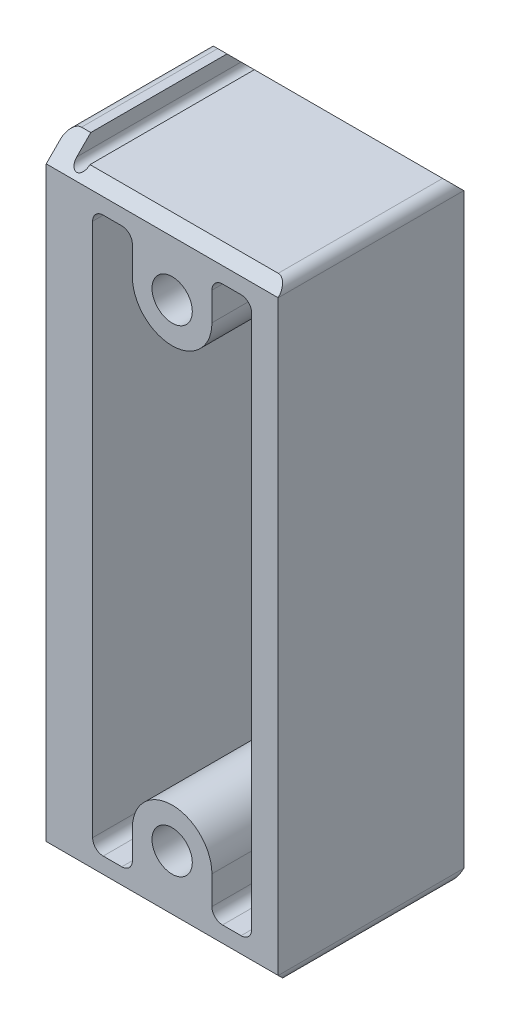
SolidWorks part; units mm, degrees
material "6061-T6 (SS)"
ref_plane "Front Plane" through (0, 0, 0) normal (0, 0, 1) x (1, 0, 0)
ref_plane "Top Plane" through (0, 0, 0) normal (0, 1, 0) x (1, 0, 0)
ref_plane "Right Plane" through (0, 0, 0) normal (1, 0, 0) x (0, 0, -1)
sketch "Sketch1" plane through (0, 0, 0) normal (0, 0, 1) x (1, 0, 0)
  line L0 (-25.4, 72.8218) -> (25.4, -72.8218) construction
  line L1 (-25.4, 72.8218) -> (25.4, 72.8218)
  line L2 (-25.4, 72.8218) -> (-25.4, -72.8218) construction
  line L3 (-25.4, -72.8218) -> (25.4, -72.8218)
  line L4 (25.4, 72.8218) -> (25.4, -72.8218)
  line L5 (0, 0) -> (47.3757, 0) construction
  line L6 (0, 57.15) -> (0, -57.15) construction
  line L7 (-25.4, 76.2) -> (-25.4, 72.8218)
  line L8 (-30.1625, 76.2) -> (-25.4, 76.2)
  line L9 (-30.1625, 76.2) -> (-30.1625, -76.2)
  line L10 (-30.1625, -76.2) -> (-25.4, -76.2)
  line L11 (-25.4, 76.2) -> (-25.4, -76.2) construction
  line L12 (-25.4, -72.8218) -> (-25.4, -76.2)
  circle A0 centre (0, 57.15) radius 4.826
  circle A1 centre (0, -57.15) radius 4.826
  point P4 (0, 0)
  point P10 (0, 0)
  point P15 (-25.4, 0)
  dimension "D6" = 9.652
  dimension "D1" = 145.6436
  dimension "D2" = 50.8
  dimension "D3" = 114.3
  dimension "D4" = 4.7625
  dimension "D5" = 152.4
extrude "Boss-Extrude1" add sketch "Sketch1" along normal mid plane 44.45
sketch "Sketch3" plane through (0, 0, 22.225) normal (0, 0, 1) x (1, 0, 0)
  line L0 (25.4, 72.8218) -> (-25.4, 72.8218) construction
  line L1 (-19.05, 66.4718) -> (-9.525, 66.4718)
  line L2 (-19.05, 66.4718) -> (-19.05, 0)
  line L3 (-19.05, 0) -> (19.05, 0)
  line L4 (19.05, 66.4718) -> (19.05, 0)
  line L5 (-9.525, 66.4718) -> (-9.525, 57.15)
  line L6 (9.525, 66.4718) -> (9.525, 57.15)
  line L7 (9.525, 66.4718) -> (19.05, 66.4718)
  arc A0 (-9.525, 57.15) -> (9.525, 57.15) centre (0, 57.15) ccw
  point P4 (0, 0)
  dimension "D3" = 19.05
  dimension "D1" = 6.35
  dimension "D2" = 6.35
extrude "Cut-Extrude2" cut sketch "Sketch3" against normal through all
sketch "Sketch4" plane through (0, 0, 22.225) normal (0, 0, 1) x (1, 0, 0)
  line L2 (25.4, 72.8218) -> (-25.4, 72.8218) construction
  line L3 (-22.225, 72.8218) -> (-25.4, 72.8218)
  line L4 (-25.4, 72.8218) -> (-25.4, 76.2) construction
  arc A0 (-25.4, 72.8218) -> (-22.225, 72.8218) centre (-23.8125, 72.8218) ccw
  dimension "D1" = 1.5875
extrude "Cut-Extrude3" cut sketch "Sketch4" against normal through all
mirror "Mirror1" about plane through (0, 0, 0) normal (0, 1, 0) of "Cut-Extrude3", "Cut-Extrude2"
fillet "Fillet1" radius 2.54 12 edges at (25.4, -72.8218, 0) (-30.1625, -76.2, 0) (19.05, -66.4718, 0) (9.525, -66.4718, 0) (-9.525, -66.4718, 0) (-19.05, -66.4718, 0) (-19.05, 66.4718, 0) (-9.525, 66.4718, 0) (9.525, 66.4718, 0) (19.05, 66.4718, 0) (25.4, 72.8218, 0) (-30.1625, 76.2, 0)
sketch "Sketch5" plane through (25.4, 0, 0) normal (1, 0, 0) x (0, 0, -1)
  line L0 (16.3068, 76.2) -> (22.225, 70.2818)
  line L1 (-22.225, 76.2) -> (22.225, 76.2) construction
  line L2 (16.3068, 76.2) -> (22.225, 76.2)
  line L3 (22.225, -70.2818) -> (22.225, 70.2818) construction
  line L4 (22.225, 70.2818) -> (22.225, 76.2)
  dimension "D1" = 45
extrude "Cut-Extrude4" cut sketch "Sketch5" against normal through all
mirror "Mirror2" about plane through (0, 0, 0) normal (0, 0, 1) of "Cut-Extrude4"
mirror "Mirror3" about plane through (0, 0, 0) normal (0, 1, 0) of "Mirror2", "Cut-Extrude4"
